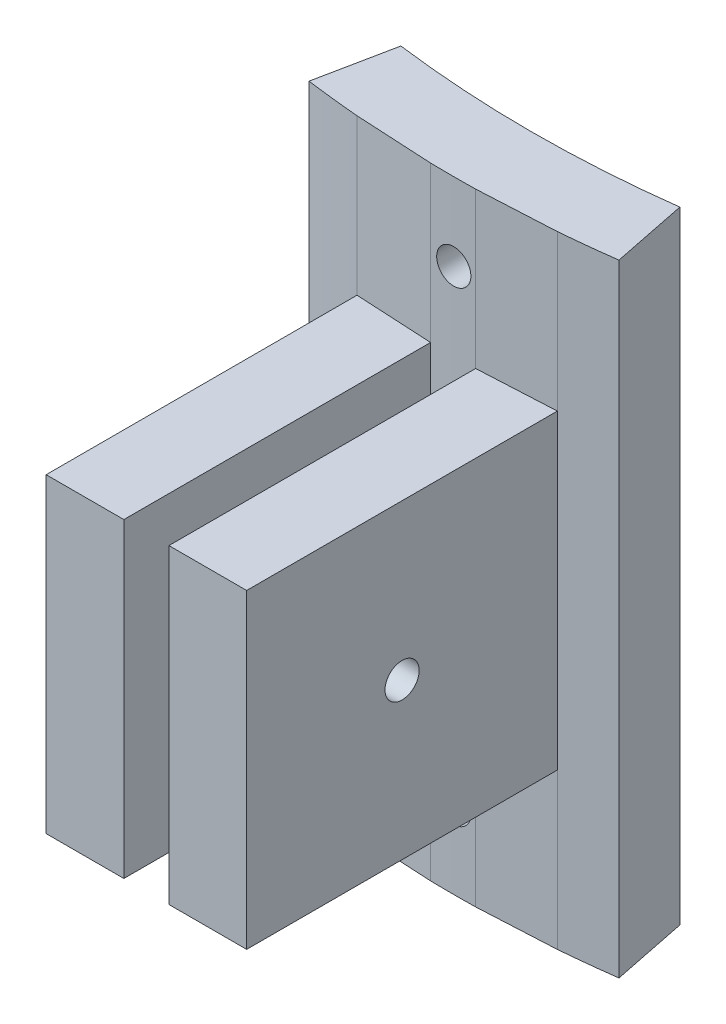
SolidWorks part; units mm, degrees
ref_plane "Front Plane" through (0, 0, 0) normal (0, 0, 1) x (1, 0, 0)
ref_plane "Top Plane" through (0, 0, 0) normal (0, 1, 0) x (1, 0, 0)
ref_plane "Right Plane" through (0, 0, 0) normal (1, 0, 0) x (0, 0, -1)
sketch "Sketch1" plane through (0, 0, 0) normal (0, 1, 0) x (1, 0, 0)
  line L0 (-8.255, -94.8916) -> (-8.255, -120.2916)
  line L1 (-8.255, -120.2916) -> (-1.905, -120.2916)
  line L2 (-1.905, -120.2916) -> (-1.905, -95.2309)
  line L3 (1.778, -95.2334) -> (1.778, -120.2916)
  line L4 (1.778, -120.2916) -> (8.128, -120.2916)
  line L5 (8.128, -120.2916) -> (8.128, -94.9026)
  line L6 (-11.3985, -88.1662) -> (-12.6624, -94.4046)
  line L7 (11.3985, -88.1662) -> (12.6624, -94.4046)
  line L8 (0, 0) -> (0, -120.2916) construction
  arc A0 (-12.6624, -94.4046) -> (-8.255, -94.8916) centre (0, 0) ccw
  arc A1 (-11.3985, -88.1662) -> (11.3985, -88.1662) centre (0, 0) ccw
  arc A2 (-1.905, -95.2309) -> (1.778, -95.2334) centre (0, 0) ccw
  arc A3 (8.128, -94.9026) -> (12.6624, -94.4046) centre (0, 0) ccw
  point P12 (0, 0)
  point P14 (0, 0)
  point P15 (0, 0)
  point P18 (0, 0)
  point P19 (0, 0)
  point P20 (0, 0)
  point P21 (0, 0)
  point P22 (0, 0)
  dimension "D1" = 95.25
  dimension "D2" = 88.9
  dimension "D4" = 22.86
  dimension "D5" = 25.4
  dimension "D3" = 3.683
  dimension "D6" = 6.35
  dimension "D7" = 1.905
  dimension "D8" = 25.4
extrude "Boss-Extrude1" add sketch "Sketch1" along normal blind 25.4
sketch "Sketch3" plane through (-8.255, 0, 0) normal (-1, 0, 0) x (0, 0, 1)
  line L0 (120.2916, 25.4) -> (120.2916, 0) construction
  line L1 (94.8916, 25.4) -> (120.2916, 25.4) construction
  circle A0 centre (107.5916, 12.7) radius 1.397
  dimension "D3" = 2.794
  dimension "D1" = 12.7
  dimension "D2" = 12.7
extrude "Cut-Extrude2" cut sketch "Sketch3" against normal blind 25.4
sketch "Sketch4" plane through (0, 25.4, 0) normal (0, 1, 0) x (1, 0, 0)
  line L0 (-8.255, -94.8916) -> (-1.905, -95.2309)
  line L1 (1.778, -95.2334) -> (8.128, -94.9026)
  line L6 (1.778, -95.2334) -> (1.778, -120.2916)
  line L8 (-8.255, -94.8916) -> (-8.255, -120.2916)
  line L9 (-8.255, -120.2916) -> (-1.905, -120.2916)
  line L10 (-1.905, -120.2916) -> (-1.905, -95.2309)
  line L15 (1.778, -120.2916) -> (8.128, -120.2916)
  line L17 (-8.255, -120.2916) -> (-1.905, -120.2916)
  line L24 (1.778, -120.2916) -> (8.128, -120.2916)
  line L25 (8.128, -120.2916) -> (8.128, -94.9026)
  line L26 (12.6624, -94.4046) -> (11.3985, -88.1662)
  line L27 (12.6624, -94.4046) -> (11.3985, -88.1662)
  line L28 (-11.3985, -88.1662) -> (-12.6624, -94.4046)
  line L29 (-11.3985, -88.1662) -> (-12.6624, -94.4046)
  arc A4 (-12.6624, -94.4046) -> (-8.255, -94.8916) centre (0, 0) ccw
  arc A5 (-12.6624, -94.4046) -> (-8.255, -94.8916) centre (0, 0) ccw
  arc A6 (-1.905, -95.2309) -> (1.778, -95.2334) centre (0, 0) ccw
  arc A7 (-1.905, -95.2309) -> (1.778, -95.2334) centre (0, 0) ccw
  arc A12 (8.128, -94.9026) -> (12.6624, -94.4046) centre (0, 0) ccw
  arc A13 (8.128, -94.9026) -> (12.6624, -94.4046) centre (0, 0) ccw
  arc A14 (-11.3985, -88.1662) -> (11.3985, -88.1662) centre (0, 0) ccw
  arc A15 (-11.3985, -88.1662) -> (11.3985, -88.1662) centre (0, 0) ccw
  arc M13 (-12.6624, -94.4046) -> (-8.255, -94.8916) centre (0, 0) ccw
  arc M17 (-1.905, -95.2309) -> (1.778, -95.2334) centre (0, 0) ccw
  arc M21 (8.128, -94.9026) -> (12.6624, -94.4046) centre (0, 0) ccw
  line M22 (12.6624, -94.4046) -> (11.3985, -88.1662)
  arc M23 (11.3985, -88.1662) -> (-11.3985, -88.1662) centre (0, 0) cw
  line M24 (-11.3985, -88.1662) -> (-12.6624, -94.4046)
  dimension "D1" = 0
extrude "Boss-Extrude2" add sketch "Sketch4" along normal blind 12.7 and the other way blind 38.1 contours L1 L0 M17 M21 M22 M23 M24 M13
sketch "Sketch5" plane through (0, 0, 120.2916) normal (0, 0, 1) x (1, 0, 0)
  line L0 (-1.905, 25.4) -> (-1.905, 0) construction
  line L1 (1.778, 38.1) -> (8.128, 38.1) construction
  circle A0 centre (0, 31.75) radius 1.397
  circle A1 centre (0, -6.35) radius 1.397
  dimension "D1" = 2.794
  dimension "D2" = 1.905
  dimension "D3" = 6.35
  dimension "D4" = 38.1
extrude "Cut-Extrude3" cut sketch "Sketch5" against normal up to surface (31.4026 mm away)
